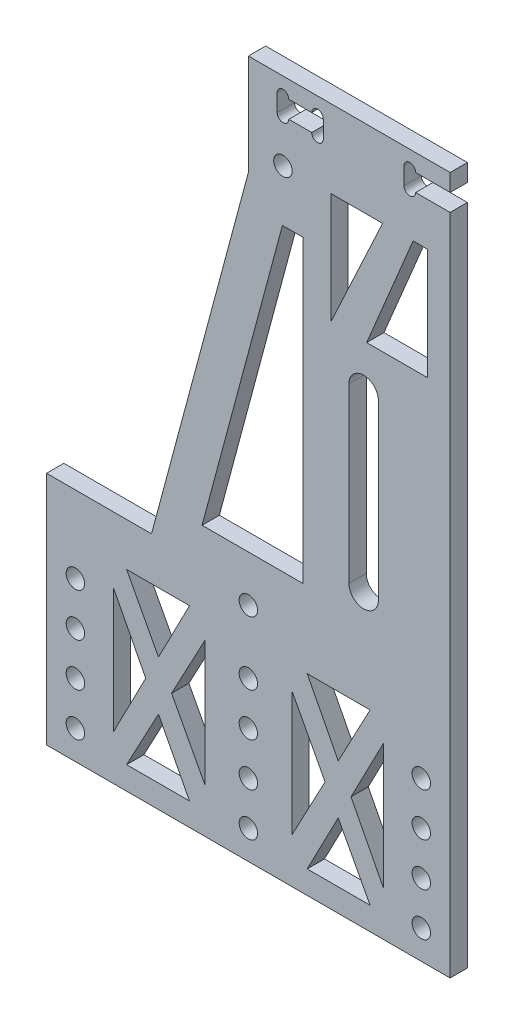
SolidWorks part; units mm, degrees
material "Thornel Mat VMA"
ref_plane "前视基准面" through (0, 0, 0) normal (0, 0, 1) x (1, 0, 0)
ref_plane "上视基准面" through (0, 0, 0) normal (0, 1, 0) x (1, 0, 0)
ref_plane "右视基准面" through (0, 0, 0) normal (1, 0, 0) x (0, 0, -1)
sketch "草图1" plane through (0, 0, 0) normal (0, 0, 1) x (1, 0, 0)
  line L0 (0, 0) -> (0, 13.7549) construction
  line L1 (0, 13.7549) -> (-30, 13.7549) construction
  line L2 (0, 13.7549) -> (0, -6.2451) construction
  line L3 (0, -6.2451) -> (20, -6.2451) construction
  line L4 (20, -6.2451) -> (20, 33.7549) construction
  line L5 (17.45, 33.7549) -> (17.45, -6.2451)
  line L6 (22.55, -6.2451) -> (22.55, 33.7549)
  line L7 (0, 33.7549) -> (0, 38.7549) construction
  line L8 (0, 38.7549) -> (-35, 38.7549) construction
  line L9 (-35, 38.7549) -> (-35, 8.7549) construction
  line L10 (-35, 8.7549) -> (0, 8.7549) construction
  line L11 (0, 38.7549) -> (-35, 38.7549)
  line L12 (-35, 38.7549) -> (-35, 13.7549)
  line L13 (-30, 8.7549) -> (-5, 8.7549)
  line L14 (0, 3.7549) -> (0, -1.2451)
  line L15 (5, -6.2451) -> (15, -6.2451)
  line L16 (0, 38.7549) -> (35, 38.7549)
  line L17 (35, 38.7549) -> (35, -1.2451)
  line L18 (30, -6.2451) -> (25, -6.2451)
  line L19 (30, 13.7549) -> (30, 33.7549) construction
  circle A0 centre (0, 13.7549) radius 1.6
  circle A1 centre (-30, 13.7549) radius 1.6
  circle A2 centre (30, 13.7549) radius 1.6
  arc A3 (17.45, -6.2451) -> (22.55, -6.2451) centre (20, -6.2451) ccw
  arc A4 (22.55, 33.7549) -> (17.45, 33.7549) centre (20, 33.7549) ccw
  circle A5 centre (-30, 23.7549) radius 1.6
  circle A6 centre (0, 23.7549) radius 1.6
  circle A7 centre (30, 23.7549) radius 1.6
  circle A8 centre (-30, 33.7549) radius 1.6
  circle A9 centre (0, 33.7549) radius 1.6
  circle A10 centre (30, 33.7549) radius 1.6
  arc A11 (15, -6.2451) -> (25, -6.2451) centre (20, -6.2451) ccw
  arc A12 (-30, 8.7549) -> (-35, 13.7549) centre (-30, 13.7549) cw
  arc A13 (35, -1.2451) -> (30, -6.2451) centre (30, -1.2451) cw
  arc A14 (0, 3.7549) -> (-5, 8.7549) centre (-5, 3.7549) ccw
  arc A15 (5, -6.2451) -> (0, -1.2451) centre (5, -1.2451) cw
  dimension "D1" = 3.2
  dimension "D3" = 3.2
  dimension "D6" = 5.1
  dimension "D8" = 5.1
  dimension "D13" = 10
  dimension "D15" = 5
  dimension "D2" = 30
  dimension "D4" = 20
  dimension "D5" = 20
  dimension "D7" = 40
  dimension "D10" = 5
  dimension "D11" = 5
  dimension "D12" = 5
  dimension "D14" = 5
  dimension "D9" = 3
extrude "凸台-拉伸2" add sketch "草图1" along normal blind 3
sketch "草图2" plane through (0, 0, 3) normal (0, 0, 1) x (1, 0, 0)
  line L0 (35, 38.7549) -> (35, 58.7549)
  line L1 (35, 58.7549) -> (-35, 58.7549)
  line L2 (-35, 58.7549) -> (-35, 38.7549)
  line L4 (-35, 38.7549) -> (35, 38.7549)
  dimension "D1" = 20
extrude "凸台-拉伸3" add sketch "草图2" against normal up to surface (3 mm away) up to face at (-28.4, 33.7549, 0)
fillet "圆角1" radius 40 2 edges at (25, -6.2451, 1.5) (15, -6.2451, 1.5)
sketch "草图4" plane through (0, 0, 3) normal (0, 0, 1) x (1, 0, 0)
  line L0 (-30, 33.7549) -> (-30, 43.7549) construction
  circle A0 centre (-30, 43.7549) radius 1.6
  circle A1 centre (0, 43.7549) radius 1.6
  circle A2 centre (30, 43.7549) radius 1.6
  dimension "D2" = 3.2
  dimension "D1" = 10
  dimension "D3" = 3
extrude "切除-拉伸1" cut sketch "草图4" against normal up to next
sketch "草图5" plane through (0, 0, 3) normal (0, 0, 1) x (1, 0, 0)
  line L0 (-30, 33.7549) -> (-30, 23.7549) construction
  line L1 (0, 33.7549) -> (0, 23.7549) construction
  line L2 (-30, 28.7549) -> (0, 28.7549) construction
  line L3 (-30, 8.7549) -> (-5, 8.7549) construction
  line L4 (-25, 43.7549) -> (-5, 43.7549)
  line L5 (-25, 43.7549) -> (-25, 13.7549)
  line L6 (-25, 13.7549) -> (-5, 13.7549)
  line L7 (-5, 43.7549) -> (-5, 13.7549)
  line L8 (-25, 43.7549) -> (-5, 13.7549) construction
  line L9 (-25, 13.7549) -> (-5, 43.7549) construction
  point P10 (-15, 28.7549)
  dimension "D1" = 5
  dimension "D2" = 5
extrude "切除-拉伸2" cut sketch "草图5" against normal up to next
sketch "草图6" plane through (0, 0, 3) normal (0, 0, 1) x (1, 0, 0)
  line L0 (-15, 43.7549) -> (-15, 13.7549)
  line L1 (-5, 43.7549) -> (-25, 43.7549) construction
  line L2 (-25, 13.7549) -> (-5, 13.7549) construction
extrude "拉伸-薄壁1" add sketch "草图6" against normal up to surface (3 mm away) thin up to face at (-15, 28.7549, 0) thin type mid plane wall 3
sketch "草图7" plane through (0, 0, 3) normal (0, 0, 1) x (1, 0, 0)
  line L0 (-25, 28.7549) -> (-5, 28.7549)
  line L1 (-25, 43.7549) -> (-25, 13.7549) construction
  line L2 (-5, 13.7549) -> (-5, 43.7549) construction
extrude "拉伸-薄壁2" add sketch "草图7" against normal up to surface (3 mm away) thin up to face at (-20.75, 28.7549, 0) thin type mid plane wall 3
sketch "草图8" plane through (0, 0, 0) normal (0, 0, -1) x (-1, 0, 0)
  line L0 (5, 13.7549) -> (25, 43.7549)
  line L1 (5, 43.7549) -> (25, 13.7549)
extrude "拉伸-薄壁3" add sketch "草图8" against normal up to surface (3 mm away) thin up to face at (-20.75, 20.5049, 3) thin type mid plane wall 3
sketch "草图9" plane through (0, 0, 3) normal (0, 0, 1) x (1, 0, 0)
  line L0 (0, 43.7549) -> (30, 43.7549) construction
  line L1 (17.45, -6.2451) -> (18.4, 43.7549) construction
  line L2 (0, 43.7549) -> (0, -6.2451) construction
  line L3 (0, -6.2451) -> (17.45, -6.2451) construction
  line L4 (0, 18.7549) -> (17.925, 18.7549) construction
  line L6 (3.9625, 38.7549) -> (13.9625, 38.7549)
  line L7 (3.9625, 38.7549) -> (3.9625, -1.2451)
  line L8 (3.9625, -1.2451) -> (13.9625, -1.2451)
  line L9 (13.9625, 38.7549) -> (13.9625, -1.2451)
  line L10 (3.9625, 38.7549) -> (13.9625, -1.2451) construction
  line L11 (3.9625, -1.2451) -> (13.9625, 38.7549) construction
  arc A0 (17.45, -6.2451) -> (22.55, -6.2451) centre (20, -6.2451) ccw construction
  point P13 (8.9625, 18.7549)
  dimension "D1" = 40
  dimension "D2" = 10
extrude "切除-拉伸3" cut sketch "草图9" against normal up to next
sketch "草图11" plane through (0, 0, 3) normal (0, 0, 1) x (1, 0, 0)
  line L0 (3.9625, 38.7549) -> (13.9625, 28.7549)
  line L1 (13.9625, -1.2451) -> (13.9625, 38.7549) construction
  line L2 (13.9625, 28.7549) -> (3.9625, 18.7549)
  line L3 (3.9625, 38.7549) -> (3.9625, -1.2451) construction
  line L4 (3.9625, 18.7549) -> (13.9625, 8.7549)
  line L5 (13.9625, 8.7549) -> (3.9625, -1.2451)
extrude "拉伸-薄壁5" add sketch "草图11" against normal up to surface (3 mm away) thin up to face at (8.9625, 18.7549, 0) thin type mid plane wall 3
sketch "草图12" plane through (0, 0, 0) normal (0, 0, -1) x (-1, 0, 0)
  line L0 (-23.7204, -1.2451) -> (-35, -1.2451) construction
  line L1 (-23.7204, -1.2451) -> (-23.7204, 11.783) construction
  line L2 (-23.7204, 11.783) -> (-35, -1.2451) construction
  line L3 (-24.7204, 9.1002) -> (-32.8115, -0.2451)
  line L4 (-24.7204, -0.2451) -> (-32.8115, -0.2451)
  line L5 (-24.7204, -0.2451) -> (-24.7204, 9.1002)
  dimension "D1" = 1
extrude "切除-拉伸4" cut sketch "草图12" against normal up to next
fillet "圆角2" radius 1 5 edges at (13.9625, -1.2451, 1.5) (13.9625, 6.6335, 1.5) (6.0838, -1.2451, 1.5) (24.7204, 9.1002, 1.5) (32.8115, -0.2451, 1.5)
sketch "草图13" plane through (0, 58.7549, 0) normal (0, 1, 0) x (1, 0, 0)
  line L4 (35, -3) -> (35, 0)
  line L5 (35, 0) -> (-35, 0)
  line L6 (-35, 0) -> (-35, -3)
  line L7 (-35, -3) -> (35, -3)
  line L8 (35, -3) -> (35, 0)
  line L9 (35, 0) -> (-35, 0)
  line L10 (-35, 0) -> (-35, -3)
  line L11 (-35, -3) -> (35, -3)
  dimension "D1" = 0
extrude "凸台-拉伸4" add sketch "草图13" along normal blind 20
sketch "草图14" plane through (0, 0, 0) normal (0, 0, -1) x (-1, 0, 0)
  line L0 (-35, 78.7549) -> (-35, 71.7549) construction
  line L1 (-35, -1.2451) -> (-35, 78.7549) construction
  line L2 (-35, 71.7549) -> (-27, 71.7549)
  line L3 (-27, 71.7549) -> (-27, 68.7549)
  line L4 (-27, 68.7549) -> (-35, 68.7549)
  line L5 (-35, 68.7549) -> (-35, 71.7549)
  line L6 (-27, 70.2549) -> (-13, 70.2549) construction
  line L7 (-20, 70.2549) -> (-20, 76.1802) construction
  line L8 (-5, 68.7549) -> (-5, 71.7549)
  line L9 (-13, 68.7549) -> (-5, 68.7549)
  line L10 (-13, 71.7549) -> (-13, 68.7549)
  line L11 (-5, 71.7549) -> (-13, 71.7549)
  dimension "D1" = 7
  dimension "D2" = 8
  dimension "D3" = 3
  dimension "D4" = 14
extrude "切除-拉伸5" cut sketch "草图14" against normal blind 3
sketch "草图15" plane through (0, 0, 3) normal (0, 0, 1) x (1, 0, 0)
  line L0 (27, 71.7549) -> (35, 71.7549) construction
  line L1 (35, 68.7549) -> (27, 68.7549) construction
  line L2 (5, 71.7549) -> (13, 71.7549) construction
  line L3 (13, 68.7549) -> (5, 68.7549) construction
  circle A0 centre (28.25, 71.7549) radius 1.25
  circle A1 centre (28.25, 68.7549) radius 1.25
  circle A2 centre (6.25, 71.7549) radius 1.25
  circle A3 centre (6.25, 68.7549) radius 1.25
  circle A4 centre (11.75, 71.7549) radius 1.25
  circle A5 centre (11.75, 68.7549) radius 1.25
  dimension "D1" = 2.5
  dimension "D2" = 2.5
  dimension "D3" = 2.5
  dimension "D4" = 2.5
  dimension "D5" = 2.5
  dimension "D6" = 2.5
extrude "切除-拉伸6" cut sketch "草图15" against normal up to next
sketch "草图16" plane through (0, 0, 3) normal (0, 0, 1) x (1, 0, 0)
  line L0 (-30, 43.7549) -> (-30, 70.2549) construction
  circle A0 centre (-30, 70.2549) radius 1.6
  dimension "D1" = 3.2
extrude "切除-拉伸7" cut sketch "草图16" against normal up to next
sketch "草图17" plane through (0, 0, 0) normal (0, 0, -1) x (-1, 0, 0)
  line L0 (30, 43.7549) -> (-30, 43.7549) construction
  line L1 (30, 70.2549) -> (-27, 70.2549) construction
  line L2 (-27, 68.7549) -> (-27, 71.7549) construction
  line L3 (0, 43.7549) -> (0, 70.2549) construction
  line L5 (-30, 64.5049) -> (30, 64.5049)
  line L6 (-30, 64.5049) -> (-30, 49.5049)
  line L7 (-30, 49.5049) -> (30, 49.5049)
  line L8 (30, 64.5049) -> (30, 49.5049)
  line L9 (-30, 64.5049) -> (30, 49.5049) construction
  line L10 (-30, 49.5049) -> (30, 64.5049) construction
  point P12 (0, 57.0049)
  dimension "D1" = 15
  dimension "D2" = 60
extrude "切除-拉伸8" cut sketch "草图17" against normal up to next
sketch "草图18" plane through (0, 0, 0) normal (0, 0, -1) x (-1, 0, 0)
  line L0 (0, 49.5049) -> (0, 64.5049)
  line L1 (-30, 49.5049) -> (30, 49.5049) construction
  line L2 (30, 64.5049) -> (-30, 64.5049) construction
  line L3 (-30, 64.5049) -> (-15, 49.5049)
  line L6 (15, 49.5049) -> (30, 64.5049)
extrude "拉伸-薄壁6" add sketch "草图18" against normal up to surface (3 mm away) thin up to face at (0, 57.0049, 3) thin type mid plane wall 3
sketch "草图19" plane through (0, 0, 0) normal (0, 0, -1) x (-1, 0, 0)
  line L0 (-1.5, 64.5049) -> (-16.5, 49.5049)
  line L1 (1.5, 64.5049) -> (16.5, 49.5049)
extrude "拉伸-薄壁8" add sketch "草图19" against normal up to surface (3 mm away) thin up to face at (-11.9636, 55.717, 3) thin type mid plane wall 3
sketch "草图20" plane through (0, 0, 0) normal (0, 0, -1) x (-1, 0, 0)
  line L0 (-30, 49.5049) -> (-23.0075, 56.4974)
  line L1 (-1.5, 49.5049) -> (-8.4925, 56.4974)
  line L2 (1.5, 49.5049) -> (8.949, 56.9539)
  line L3 (30, 49.5049) -> (22.551, 56.9539)
  line L4 (15.75, 52.3762) -> (15.75, 66.7549)
  line L5 (-15.75, 52.3762) -> (-15.75, 65.5377)
extrude "拉伸-薄壁9" add sketch "草图20" against normal up to surface (3 mm away) thin up to face at (-5.7929, 53.7977, 3) thin type mid plane wall 2
sketch "草图21" plane through (0, 0, 0) normal (0, 0, -1) x (-1, 0, 0)
  line L0 (-20, 55.7549) -> (-20, 25.7549) construction
  line L1 (-17.45, 55.7549) -> (-17.45, 25.7549)
  line L2 (-22.55, 55.7549) -> (-22.55, 25.7549)
  line L3 (-17.45, 33.7549) -> (-17.45, -6.2451) construction
  line L4 (-22.55, -6.2451) -> (-22.55, 33.7549) construction
  arc A0 (-17.45, 55.7549) -> (-22.55, 55.7549) centre (-20, 55.7549) ccw
  arc A1 (-22.55, 25.7549) -> (-17.45, 25.7549) centre (-20, 25.7549) ccw
  circle A2 centre (0, 13.7549) radius 1.6 construction
  point P2 (-20, 40.7549)
  dimension "D1" = 42
  dimension "D2" = 30
extrude "切除-拉伸9" cut sketch "草图21" against normal through all
sketch "草图22" plane through (0, 0, 0) normal (0, 0, -1) x (-1, 0, 0)
  line L0 (-24.7204, -0.2451) -> (-24.7204, 6.4174) construction
  line L1 (-14.6614, 64.5049) -> (-24.7204, 64.5049)
  line L2 (-17.45, 25.7549) -> (-17.45, 55.7549)
  line L3 (-22.55, 55.7549) -> (-22.55, 25.7549)
  line L4 (-17.45, 25.7549) -> (-17.45, 55.7549)
  line L5 (-22.55, 55.7549) -> (-22.55, 25.7549)
  line L6 (-14.6614, 64.5049) -> (-14.6614, -9.1861)
  line L7 (-14.6614, -9.1861) -> (-24.7204, -9.1861)
  line L8 (-24.7204, 64.5049) -> (-24.7204, -9.1861)
  line L10 (-16.75, 64.5049) -> (-27.8787, 64.5049) construction
  arc A0 (-22.7743, -10.4049) -> (-31.6632, -5.9604) centre (-44.9687, -43.6826) ccw construction
  arc A1 (-4.2768, -6.1926) -> (-17.6101, -10.637) centre (1.5089, -45.7719) ccw construction
  arc A2 (-22.55, 25.7549) -> (-17.45, 25.7549) centre (-20, 25.7549) ccw
  arc A3 (-17.45, 55.7549) -> (-22.55, 55.7549) centre (-20, 55.7549) ccw
  arc A4 (-22.55, 25.7549) -> (-17.45, 25.7549) centre (-20, 25.7549) ccw
  arc A5 (-17.45, 55.7549) -> (-22.55, 55.7549) centre (-20, 55.7549) ccw
  dimension "D1" = 0
extrude "凸台-拉伸5" add sketch "草图22" against normal up to surface (3 mm away) up to face at (11.0404, 60.7953, 3)
sketch "草图23" plane through (0, 0, 0) normal (0, 0, -1) x (-1, 0, 0)
  line L0 (-35, -1.2451) -> (-35, 68.7549) construction
  line L1 (-35, 67.5049) -> (0, 67.5049)
  line L2 (-35, 67.5049) -> (-35, 90.2549)
  line L3 (-35, 96.2549) -> (0, 96.2549)
  line L4 (0, 67.5049) -> (0, 96.2549)
  line L5 (-5, 68.7549) -> (-5, 71.7549) construction
  line L7 (-27, 68.7549) -> (-27, 71.7549) construction
  line L8 (-35, 93.2549) -> (-27, 93.2549)
  line L10 (-35, 90.2549) -> (-27, 90.2549)
  line L11 (-27, 93.2549) -> (-27, 90.2549)
  line L12 (-13, 93.2549) -> (-5, 93.2549)
  line L13 (-13, 93.2549) -> (-13, 90.2549)
  line L14 (-13, 90.2549) -> (-5, 90.2549)
  line L15 (-5, 93.2549) -> (-5, 90.2549)
  line L16 (-13, 71.7549) -> (-13, 68.7549) construction
  line L17 (-29.5, 71.7549) -> (-35, 71.7549) construction
  line L18 (-35, 93.2549) -> (-35, 96.2549)
  arc A0 (-13, 68.7549) -> (-10.5, 68.7549) centre (-11.75, 68.7549) ccw construction
  dimension "D1" = 5
  dimension "D2" = 21.5
  dimension "D3" = 3
extrude "凸台-拉伸6" add sketch "草图23" against normal up to surface (3 mm away) up to face at (25.7732, 63.4521, 3)
sketch "草图24" plane through (0, 0, 0) normal (0, 0, -1) x (-1, 0, 0)
  line L0 (-35, 93.2549) -> (-27, 93.2549) construction
  line L1 (-27, 90.2549) -> (-35, 90.2549) construction
  line L2 (-5, 93.2549) -> (-13, 93.2549) construction
  line L3 (-13, 90.2549) -> (-5, 90.2549) construction
  circle A0 centre (-28.005, 93.2549) radius 1.005
  circle A1 centre (-28.005, 90.2549) radius 1.005
  circle A2 centre (-11.995, 93.2549) radius 1.005
  circle A3 centre (-11.995, 90.2549) radius 1.005
  circle A4 centre (-6.005, 90.2549) radius 1.005
  circle A5 centre (-6.005, 93.2549) radius 1.005
  dimension "D1" = 2.01
extrude "切除-拉伸10" cut sketch "草图24" against normal through all
sketch "草图25" plane through (0, 0, 0) normal (0, 0, -1) x (-1, 0, 0)
  line L1 (-25.4602, 69.5049) -> (-9.5398, 69.5049)
  line L2 (-30, 69.5049) -> (-30, 85.2549)
  line L3 (-25.1605, 85.2549) -> (-9.8395, 85.2549)
  line L4 (-5, 69.5049) -> (-5, 85.2549)
  line L5 (-31.7654, 73.3098) -> (-6.2943, 91.3943) construction
  line L6 (-30, 89.2549) -> (-5, 69.5049) construction
  line L7 (0, 78.7549) -> (0, 96.2549) construction
  line L8 (-35, -1.2451) -> (-35, 90.2549) construction
  line L9 (-3.6213, 64.5049) -> (-14.6614, 64.5049) construction
  line L10 (-10.99, 90.2549) -> (-7.01, 90.2549) construction
  line L11 (-30, 85.2549) -> (-19.5, 76.9599)
  line L12 (-19.5, 76.9599) -> (-30, 69.5049)
  line L13 (-25.1605, 85.2549) -> (-17.5, 79.2031)
  line L14 (-17.5, 75.1566) -> (-25.4602, 69.5049)
  line L15 (-17.5, 89.2549) -> (-17.5, 69.5049) construction
  line L16 (-17.5, 75.1566) -> (-9.5398, 69.5049)
  line L17 (-15.5, 76.9599) -> (-5, 69.5049)
  line L18 (-5, 85.2549) -> (-15.5, 76.9599)
  line L19 (-9.8395, 85.2549) -> (-17.5, 79.2031)
  point P0 (-20.2056, 81.5173)
  dimension "D1" = 5
  dimension "D2" = 5
  dimension "D3" = 5
  dimension "D4" = 5
  dimension "D5" = 3
  dimension "D6" = 4
extrude "切除-拉伸11" cut sketch "草图25" against normal through all
sketch "草图26" plane through (0, 0, 0) normal (0, 0, -1) x (-1, 0, 0)
  line L0 (-35, -1.2451) -> (-35, 90.2549) construction
  line L1 (35, 13.7549) -> (31.6, 13.7549)
  line L2 (35, 13.7549) -> (35, -31.2451)
  line L3 (35, -31.2451) -> (-35, -31.2451)
  line L4 (-35, 13.7549) -> (-35, -31.2451)
  line L5 (-31.6, 13.7549) -> (-35, 13.7549)
  line L6 (-1.6, 13.7549) -> (-28.4, 13.7549)
  line L7 (28.4, 13.7549) -> (1.6, 13.7549)
  circle A0 centre (-30, 13.7549) radius 1.6 construction
  circle A1 centre (0, 13.7549) radius 1.6 construction
  circle A2 centre (30, 13.7549) radius 1.6 construction
  arc A3 (-31.6, 13.7549) -> (-28.4, 13.7549) centre (-30, 13.7549) ccw
  arc A4 (-1.6, 13.7549) -> (1.6, 13.7549) centre (0, 13.7549) ccw
  arc A5 (28.4, 13.7549) -> (31.6, 13.7549) centre (30, 13.7549) ccw
  dimension "D1" = 45
extrude "凸台-拉伸7" add sketch "草图26" against normal up to surface (3 mm away) up to face at (8.5, 77.2399, 3)
sketch "草图27" plane through (0, 0, 0) normal (0, 0, -1) x (-1, 0, 0)
  line L0 (-30, 13.7549) -> (-30, 2.7549) construction
  circle A0 centre (-30, 13.7549) radius 1.6 construction
  circle A1 centre (0, 13.7549) radius 1.6 construction
  circle A2 centre (30, 13.7549) radius 1.6 construction
  circle A3 centre (-30, 13.7549) radius 1.6
  circle A4 centre (0, 13.7549) radius 1.6
  circle A5 centre (30, 13.7549) radius 1.6
  circle A6 centre (-30, 2.7549) radius 1.6
  circle A7 centre (0, 2.7549) radius 1.6
  circle A8 centre (30, 2.7549) radius 1.6
  circle A9 centre (-30, -4.7451) radius 1.6
  circle A10 centre (0, -4.7451) radius 1.6
  circle A11 centre (30, -4.7451) radius 1.6
  circle A12 centre (-30, -12.2451) radius 1.6
  circle A13 centre (0, -12.2451) radius 1.6
  circle A14 centre (30, -12.2451) radius 1.6
  circle A15 centre (-30, -19.7451) radius 1.6
  circle A16 centre (0, -19.7451) radius 1.6
  circle A17 centre (30, -19.7451) radius 1.6
  dimension "D4" = 7.5
  dimension "D2" = 11
  dimension "D1" = 2
  dimension "D3" = 4
extrude "切除-拉伸12" cut sketch "草图27" against normal through all
sketch "草图28" plane through (0, 0, 0) normal (0, 0, -1) x (-1, 0, 0)
  line L0 (-35, -31.2451) -> (-35, 90.2549) construction
  line L1 (35, -31.2451) -> (-35, -31.2451)
  line L2 (35, -31.2451) -> (35, -24.7451)
  line L3 (35, -24.7451) -> (-35, -24.7451)
  line L4 (-35, -31.2451) -> (-35, -24.7451)
  line L5 (0, 8.5752) -> (0, -37.3628) construction
  line L6 (21.1156, 8.5752) -> (10.2069, 8.5752)
  line L7 (23.4186, 4.6966) -> (23.4186, -16.9998)
  line L8 (21.1156, -20.7572) -> (10.2069, -20.7572)
  line L9 (7.5403, 4.6966) -> (7.5403, -16.9998)
  line L10 (10.2069, 8.5752) -> (15.5872, -1.8399)
  line L11 (7.5403, 4.6966) -> (13.3122, -6.1258)
  line L12 (21.1156, 8.5752) -> (15.5872, -1.8399)
  line L13 (23.4186, 4.6966) -> (17.8013, -6.1258)
  line L14 (17.8013, -6.1258) -> (23.4186, -16.9998)
  line L15 (13.3122, -6.1258) -> (7.5403, -16.9998)
  line L16 (15.5872, -10.3914) -> (21.1156, -20.7572)
  line L17 (15.5872, -10.3914) -> (10.2069, -20.7572)
  line L18 (-15.5872, -10.3914) -> (-10.2069, -20.7572)
  line L19 (-15.5872, -10.3914) -> (-21.1156, -20.7572)
  line L20 (-13.3122, -6.1258) -> (-7.5403, -16.9998)
  line L21 (-17.8013, -6.1258) -> (-23.4186, -16.9998)
  line L22 (-23.4186, 4.6966) -> (-17.8013, -6.1258)
  line L23 (-21.1156, 8.5752) -> (-15.5872, -1.8399)
  line L24 (-7.5403, 4.6966) -> (-13.3122, -6.1258)
  line L25 (-10.2069, 8.5752) -> (-15.5872, -1.8399)
  line L26 (-7.5403, 4.6966) -> (-7.5403, -16.9998)
  line L27 (-21.1156, -20.7572) -> (-10.2069, -20.7572)
  line L28 (-23.4186, 4.6966) -> (-23.4186, -16.9998)
  line L29 (-21.1156, 8.5752) -> (-10.2069, 8.5752)
  circle A0 centre (-30, -19.7451) radius 1.6 construction
  dimension "D1" = 5
extrude "切除-拉伸13" cut sketch "草图28" against normal through all
sketch "草图31" plane through (0, 0, 3) normal (0, 0, 1) x (1, 0, 0)
  line L0 (-35, 78.7549) -> (-35, 9.8737)
  line L1 (-35, 78.7549) -> (-35, -24.7451) construction
  line L2 (-35, 9.8737) -> (-4.0074, 9.8737)
  line L3 (-4.0074, 9.8737) -> (-4.0074, 17.0536)
  line L4 (-4.0074, 17.0536) -> (2.8386, 17.0536)
  line L5 (2.8386, 17.0536) -> (2.8386, 9.8737)
  line L6 (2.8386, 9.8737) -> (15.6957, 9.8737)
  line L7 (15.6957, 9.8737) -> (15.6957, 61.469)
  line L8 (15.6957, 61.469) -> (23.2095, 61.469)
  line L9 (23.2095, 61.469) -> (23.2095, 9.8737)
  line L10 (23.2095, 9.8737) -> (35, 9.8737)
  line L11 (35, -24.7451) -> (35, 90.2549) construction
  line L12 (35, 9.8737) -> (35, 86.6823)
  line L13 (35, 86.6823) -> (0, 86.6823)
  line L14 (0, 96.2549) -> (0, 78.7549) construction
  line L15 (0, 86.6823) -> (0, 78.7549)
  line L16 (0, 78.7549) -> (-35, 78.7549)
extrude "凸台-拉伸8" add sketch "草图31" against normal up to surface (3 mm away) up to face at (15.6366, 5.1035, 0)
sketch "草图32" plane through (0, 0, 3) normal (0, 0, 1) x (1, 0, 0)
  line L0 (0, 78.7549) -> (-16.795, 16.0752)
  line L1 (-16.795, 16.0752) -> (-35, 16.0752)
  line L2 (-35, 78.7549) -> (-35, -24.7451) construction
  line L3 (-35, 16.0752) -> (-35, 78.7549)
  line L4 (-35, 78.7549) -> (0, 78.7549)
  line L5 (-21.1156, 8.5752) -> (-10.2069, 8.5752) construction
  line L6 (0, 96.2549) -> (0, 78.7549) construction
  line L7 (7.01, 90.2549) -> (10.99, 90.2549) construction
  line L8 (5.9072, 73.7549) -> (-8.0262, 21.7549)
  line L10 (-8.0262, 21.7549) -> (9.45, 21.7549)
  line L11 (9.45, 21.7549) -> (9.45, 73.7549)
  line L12 (9.45, 73.7549) -> (5.9072, 73.7549)
  line L13 (17.45, 55.7549) -> (17.45, 25.7549) construction
  line L14 (14.3118, 82.7549) -> (14.3118, 63.4686)
  line L15 (14.3118, 63.4686) -> (23.2841, 82.7549)
  line L16 (23.2841, 82.7549) -> (14.3118, 82.7549)
  line L18 (28.5754, 82.7549) -> (20.5234, 63.4686)
  line L19 (20.5234, 63.4686) -> (31.106, 63.4686)
  line L20 (31.106, 63.4686) -> (31.106, 82.7549)
  line L21 (31.106, 82.7549) -> (28.5754, 82.7549)
  circle A0 centre (6, 82.7549) radius 1.6
  circle A1 centre (0, 13.7549) radius 1.6 construction
  point P3 (-15.6613, 8.5752)
  dimension "D4" = 3.2
  dimension "D5" = 7.5
  dimension "D6" = 9
  dimension "D1" = 7.5
  dimension "D2" = 75
  dimension "D3" = 6
  dimension "D7" = 7
  dimension "D8" = 8
  dimension "D9" = 8
extrude "切除-拉伸15" cut sketch "草图32" against normal through all
